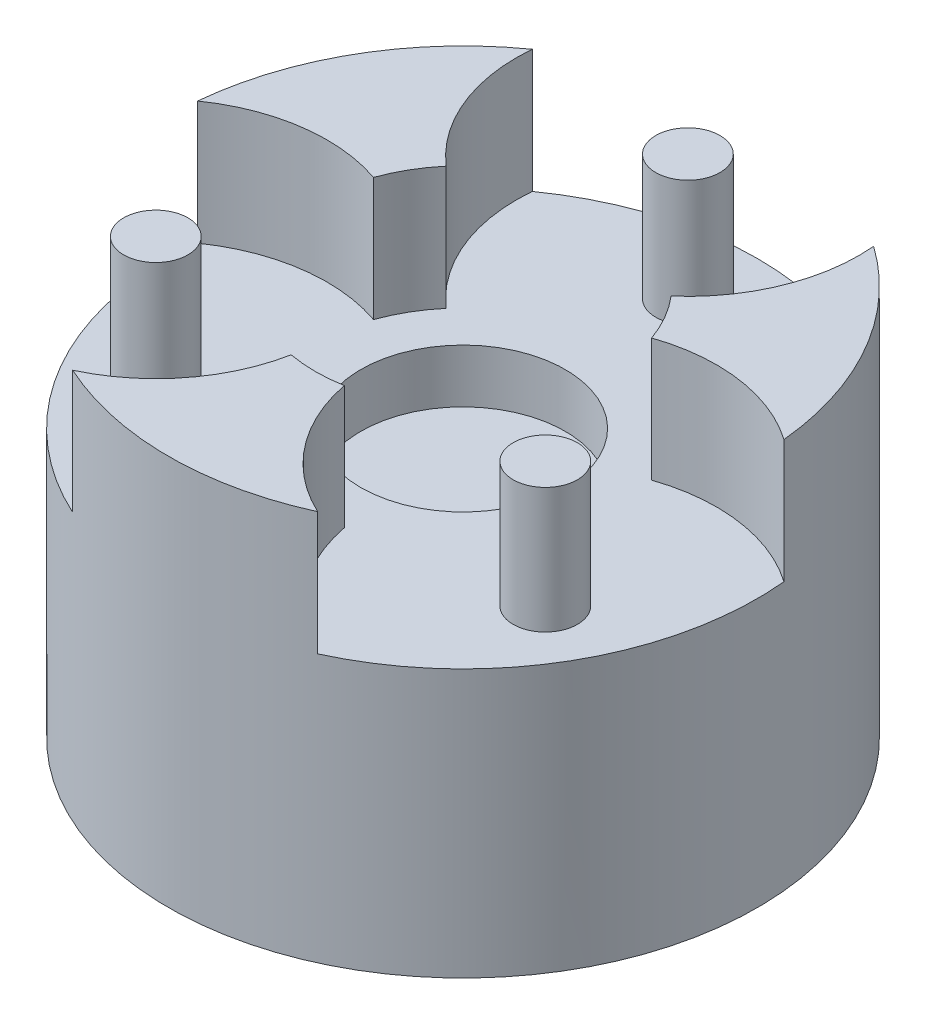
SolidWorks part; units mm, degrees
ref_plane "Front Plane" through (0, 0, 0) normal (0, 0, 1) x (1, 0, 0)
ref_plane "Top Plane" through (0, 0, 0) normal (0, 1, 0) x (1, 0, 0)
ref_plane "Right Plane" through (0, 0, 0) normal (1, 0, 0) x (0, 0, -1)
sketch "Sketch1" plane through (0, 0, 0) normal (0, 1, 0) x (1, 0, 0)
  circle A0 centre (0, 0) radius 9.55
  circle A1 centre (0, 0) radius 21 construction
  circle A2 centre (0, 0) radius 27.5
  dimension "D1" = 19.1
  dimension "D2" = 42
  dimension "D3" = 55
extrude "Boss-Extrude1" add sketch "Sketch1" along normal blind 5
sketch "Sketch2" plane through (0, 5, 0) normal (0, 1, 0) x (1, 0, 0)
  circle A0 centre (0, 0) radius 21 construction
  circle A1 centre (0, 21) radius 3
  circle A2 centre (18.1865, -10.5) radius 3
  circle A3 centre (-18.1865, -10.5) radius 3
  point P11 (0, 0)
  dimension "D1" = 42
  dimension "D2" = 3
  dimension "D3" = 6
extrude "Boss-Extrude2" add sketch "Sketch2" along normal blind 11.7
sketch "Sketch3" plane through (0, 5, 0) normal (0, 1, 0) x (1, 0, 0)
  arc A0 (-15.9377, 22.4107) -> (-10.5047, 8.9314) centre (0, 21) ccw
  arc A1 (-12.9871, 4.6316) -> (-27.3771, 2.5971) centre (-18.1865, -10.5) ccw
  arc A2 (2.4825, -13.563) -> (11.4394, -25.0078) centre (18.1865, -10.5) ccw
  arc A3 (-10.5047, 8.9314) -> (-12.9871, 4.6316) centre (0, 0) ccw
  arc A4 (-15.9377, 22.4107) -> (-27.3771, 2.5971) centre (0, 0) ccw
  arc A5 (10.5047, 8.9314) -> (15.9377, 22.4107) centre (0, 21) ccw
  arc A6 (-2.4825, -13.563) -> (2.4825, -13.563) centre (0, 0) ccw
  arc A7 (-11.4394, -25.0078) -> (11.4394, -25.0078) centre (0, 0) ccw
  arc A8 (-11.4394, -25.0078) -> (-2.4825, -13.563) centre (-18.1865, -10.5) ccw
  arc A9 (12.9871, 4.6316) -> (10.5047, 8.9314) centre (0, 0) ccw
  arc A10 (27.3771, 2.5971) -> (12.9871, 4.6316) centre (18.1865, -10.5) ccw
  arc A11 (27.3771, 2.5971) -> (15.9377, 22.4107) centre (0, 0) ccw
  circle A15 centre (0, 0) radius 27.5 construction
  point P28 (0, 0)
  dimension "D2" = 16
  dimension "D3" = 16
extrude "Boss-Extrude3" add sketch "Sketch3" along normal blind 11.5
sketch "Sketch6" plane through (0, 0, 0) normal (0, -1, 0) x (1, 0, 0)
  circle A0 centre (0, 0) radius 27.5
extrude "Boss-Extrude4" add sketch "Sketch6" along normal blind 20
